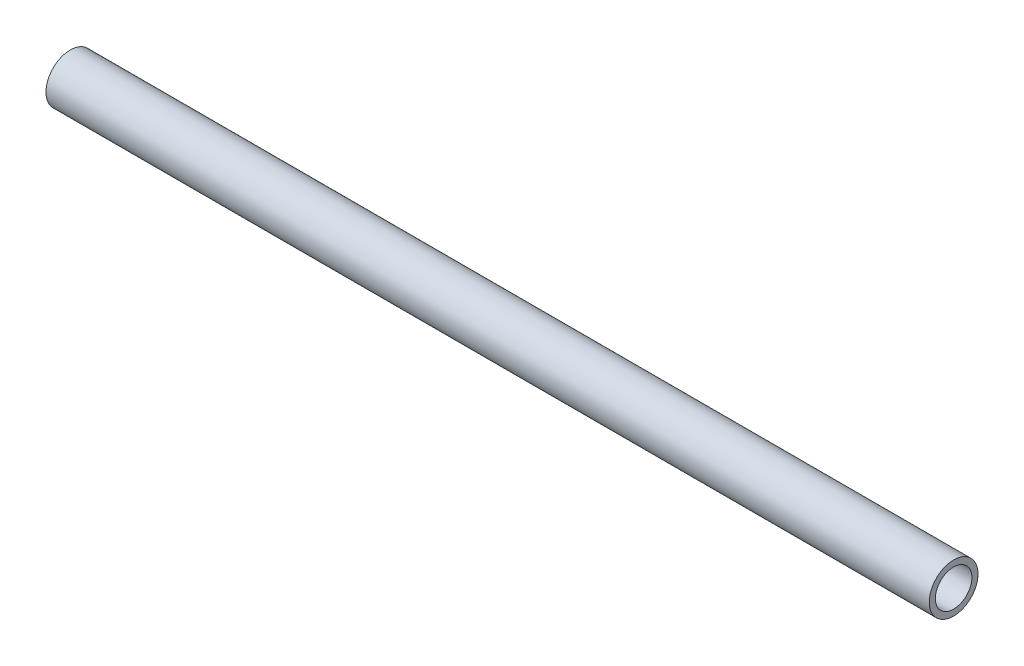
SolidWorks part; units mm, degrees
material "1.0037 (S235JR)"
ref_plane "Front Plane" through (0, 0, 0) normal (0, 0, 1) x (1, 0, 0)
ref_plane "Top Plane" through (0, 0, 0) normal (0, 1, 0) x (1, 0, 0)
ref_plane "Right Plane" through (0, 0, 0) normal (1, 0, 0) x (0, 0, -1)
sketch "Sketch1" plane through (0, 0, 0) normal (1, 0, 0) x (0, 0, -1)
  circle A0 centre (0, 0) radius 8
  circle A1 centre (0, 0) radius 6
  dimension "D1" = 16
  dimension "D2" = 2
extrude "Boss-Extrude1" add sketch "Sketch1" along normal mid plane 290
